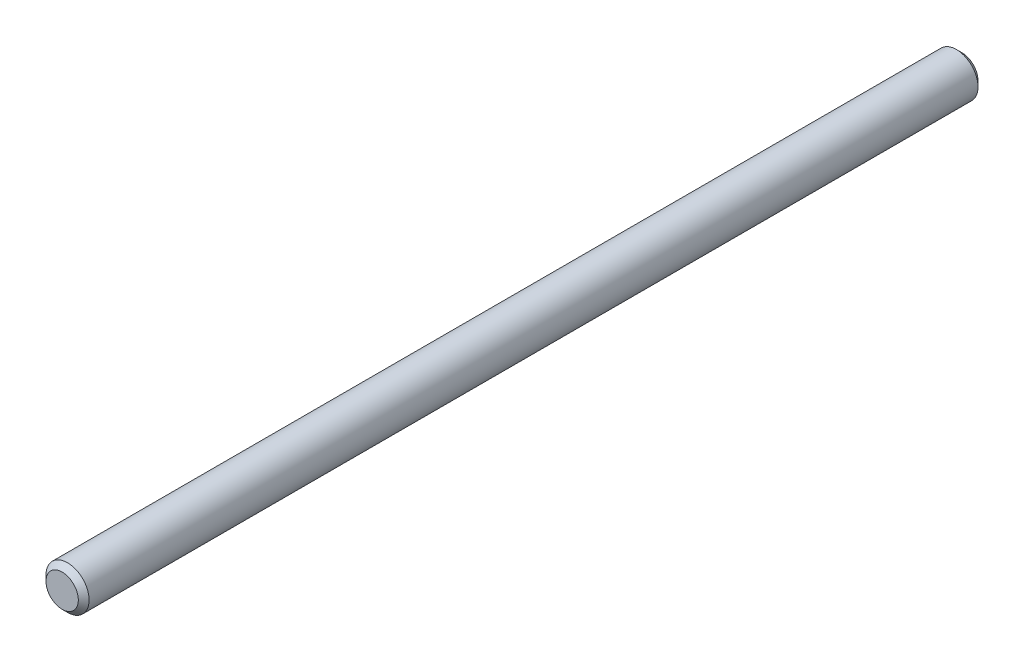
SolidWorks part; units mm, degrees
ref_plane "Piano frontale" through (0, 0, 0) normal (0, 0, 1) x (1, 0, 0)
ref_plane "Piano superiore" through (0, 0, 0) normal (0, 1, 0) x (1, 0, 0)
ref_plane "Piano destro" through (0, 0, 0) normal (1, 0, 0) x (0, 0, -1)
ref_plane "Plane1" through (0, 0, 64.8812) normal (0, 0, -1) x (-1, 0, 0)
sketch "Schizzo1" plane through (0, 0, 64.8812) normal (0, 0, 1) x (1, 0, 0)
  circle A0 centre (0, 0) radius 4
  dimension "D1" = 8
extrude "Estrusione-Estrusione1" add sketch "Schizzo1" along normal up to surface (167 mm away)
chamfer "Smusso1" distance 1 angle 45
